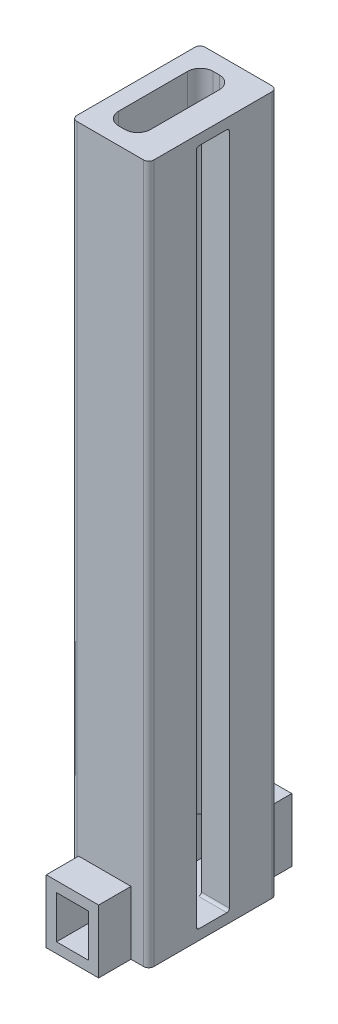
SolidWorks part; units mm, degrees
ref_plane "Front Plane" through (0, 0, 0) normal (0, 0, 1) x (1, 0, 0)
ref_plane "Top Plane" through (0, 0, 0) normal (0, 1, 0) x (1, 0, 0)
ref_plane "Right Plane" through (0, 0, 0) normal (1, 0, 0) x (0, 0, -1)
sketch "Sketch3" plane through (0, 0, 0) normal (0, 1, 0) x (1, 0, 0)
  line L0 (0, -11.5) -> (0, 11.5)
  line L1 (1, 12.5) -> (14, 12.5)
  line L2 (15, 11.5) -> (15, 3.2)
  line L3 (15, 3.2) -> (9.55, 3.2)
  line L4 (9.55, 3.2) -> (9.55, 6.7)
  line L5 (7.05, 9.2) -> (5.85, 9.2)
  line L6 (1, -12.5) -> (14, -12.5)
  line L7 (15, -11.5) -> (15, -3.2)
  line L8 (15, -3.2) -> (9.55, -3.2)
  line L9 (9.55, -3.2) -> (9.55, -6.7)
  line L10 (7.05, -9.2) -> (5.85, -9.2)
  line L11 (3.35, -6.7) -> (3.35, 6.7)
  arc A0 (9.55, -6.7) -> (7.05, -9.2) centre (7.05, -6.7) cw
  arc A1 (9.55, 6.7) -> (7.05, 9.2) centre (7.05, 6.7) ccw
  arc A2 (5.85, 9.2) -> (3.35, 6.7) centre (5.85, 6.7) ccw
  arc A3 (5.85, -9.2) -> (3.35, -6.7) centre (5.85, -6.7) cw
  arc A4 (0, -11.5) -> (1, -12.5) centre (1, -11.5) ccw
  arc A5 (14, -12.5) -> (15, -11.5) centre (14, -11.5) ccw
  arc A6 (14, 12.5) -> (15, 11.5) centre (14, 11.5) cw
  arc A7 (0, 11.5) -> (1, 12.5) centre (1, 11.5) cw
  point P4 (0, 0)
  point P17 (9.55, -9.2)
  point P20 (9.55, 9.2)
  point P23 (3.35, 9.2)
  point P26 (3.35, -9.2)
  point P29 (0, -12.5)
  point P32 (15, -12.5)
  point P35 (15, 12.5)
  point P38 (0, 12.5)
  dimension "D11" = 2.5
  dimension "D12" = 1
  dimension "D1" = 25
  dimension "D2" = 15
  dimension "D3" = 15
  dimension "D4" = 6.2
  dimension "D5" = 6.2
  dimension "D6" = 18.4
  dimension "D7" = 3.3
  dimension "D8" = 6
  dimension "D9" = 6
  dimension "D10" = 3.35
extrude "Boss-Extrude2" add sketch "Sketch3" along normal blind 134
sketch "Sketch6" plane through (0, 0, 0) normal (0, -1, 0) x (1, 0, 0)
  line L0 (1, 12.5) -> (3.35, 12.5)
  line L1 (15, 11.5) -> (15, -11.5)
  line L2 (14, -12.5) -> (9.55, -12.5)
  line L3 (0, -11.5) -> (0, 11.5)
  line L4 (0, -11.5) -> (0, 11.5) construction
  line L5 (6.45, 12.5) -> (6.45, 18.8) construction
  line L7 (6.45, -12.5) -> (6.45, -18.8) construction
  line L8 (1, 12.5) -> (14, 12.5) construction
  line L9 (3.35, 18.8) -> (9.55, 18.8)
  line L10 (9.55, 18.8) -> (9.55, 12.5)
  line L12 (3.35, 18.8) -> (3.35, 12.5)
  line L13 (3.35, -18.8) -> (9.55, -18.8)
  line L14 (9.55, -18.8) -> (9.55, -12.5)
  line L15 (3.35, -18.8) -> (3.35, -12.5)
  line L16 (9.55, 12.5) -> (14, 12.5)
  line L17 (3.35, -12.5) -> (1, -12.5)
  line L18 (3.35, 6.7) -> (3.35, -6.7) construction
  line L19 (9.55, 3.2) -> (9.55, 6.7) construction
  line L20 (9.55, -6.7) -> (9.55, -3.2) construction
  arc A0 (1, -12.5) -> (0, -11.5) centre (1, -11.5) cw
  arc A1 (15, -11.5) -> (14, -12.5) centre (14, -11.5) cw
  arc A2 (14, 12.5) -> (15, 11.5) centre (14, 11.5) cw
  arc A3 (1, 12.5) -> (0, 11.5) centre (1, 11.5) ccw
  point P8 (0, -12.5)
  point P13 (15, 12.5)
  point P16 (0, 12.5)
  point P26 (6.45, 18.8)
  point P31 (6.45, -18.8)
  dimension "D3" = 1
  dimension "D1" = 15
  dimension "D2" = 25
  dimension "D5" = 6.3
  dimension "D7" = 6.3
extrude "Boss-Extrude3" add sketch "Sketch6" along normal blind 2
sketch "Sketch7" plane through (0, 0, 12.5) normal (0, 0, 1) x (1, 0, 0)
  line L0 (3.35, 0) -> (3.35, 8.35)
  line L1 (3.35, 8.35) -> (9.55, 8.35)
  line L2 (9.55, 8.35) -> (9.55, 0)
  line L3 (3.35, 0) -> (9.55, 0)
  dimension "D1" = 8.35
extrude "Cut-Extrude5" [suppressed] cut sketch "Sketch7" against normal through all
sketch "Sketch18" plane through (0, 134, 0) normal (0, 1, 0) x (1, 0, 0)
  line L0 (9.55, 3.2) -> (9.55, -3.2)
  line L1 (9.55, -3.2) -> (15, -3.2)
  line L2 (15, -3.2) -> (15, 3.2)
  line L3 (15, 3.2) -> (9.55, 3.2)
extrude "Boss-Extrude10" add sketch "Sketch18" against normal blind 2
fillet "Fillet1" radius 0.5 1 edges at (12.275, 132, 3.2)
fillet "Fillet2" radius 0.5 3 edges at (12.275, 0, 3.2) (12.275, 132, -3.2) (12.275, 0, -3.2)
sketch "Sketch43" plane through (0, -2, 0) normal (0, 1, 0) x (1, 0, 0)
  line L12 (9.55, 12.5) -> (9.55, 18.8)
  line L13 (9.55, 18.8) -> (3.35, 18.8)
  line L14 (3.35, 18.8) -> (3.35, 12.5)
  line L15 (3.35, 12.5) -> (1, 12.5)
  line L16 (0, 11.5) -> (0, -11.5)
  line L17 (1, -12.5) -> (3.35, -12.5)
  line L18 (3.35, -12.5) -> (3.35, -18.8)
  line L19 (3.35, -18.8) -> (9.55, -18.8)
  line L20 (9.55, -18.8) -> (9.55, -12.5)
  line L21 (9.55, -12.5) -> (14, -12.5)
  line L22 (15, -11.5) -> (15, 11.5)
  line L23 (14, 12.5) -> (9.55, 12.5)
  line L24 (9.55, 12.5) -> (9.55, 18.8)
  line L25 (9.55, 18.8) -> (3.35, 18.8)
  line L26 (3.35, 18.8) -> (3.35, 12.5)
  line L27 (3.35, 12.5) -> (1, 12.5)
  line L28 (0, 11.5) -> (0, -11.5)
  line L29 (1, -12.5) -> (3.35, -12.5)
  line L30 (3.35, -12.5) -> (3.35, -18.8)
  line L31 (3.35, -18.8) -> (9.55, -18.8)
  line L32 (9.55, -18.8) -> (9.55, -12.5)
  line L33 (9.55, -12.5) -> (14, -12.5)
  line L34 (15, -11.5) -> (15, 11.5)
  line L35 (14, 12.5) -> (9.55, 12.5)
  arc A4 (1, 12.5) -> (0, 11.5) centre (1, 11.5) ccw
  arc A5 (0, -11.5) -> (1, -12.5) centre (1, -11.5) ccw
  arc A6 (14, -12.5) -> (15, -11.5) centre (14, -11.5) ccw
  arc A7 (15, 11.5) -> (14, 12.5) centre (14, 11.5) ccw
  arc A8 (1, 12.5) -> (0, 11.5) centre (1, 11.5) ccw
  arc A9 (0, -11.5) -> (1, -12.5) centre (1, -11.5) ccw
  arc A10 (14, -12.5) -> (15, -11.5) centre (14, -11.5) ccw
  arc A11 (15, 11.5) -> (14, 12.5) centre (14, 11.5) ccw
  dimension "D1" = 0
sketch "Sketch44" plane through (0, -2, 0) normal (0, -1, 0) x (1, 0, 0)
sketch "Sketch45" plane through (0, 0, -12.5) normal (0, 0, -1) x (-1, 0, 0)
  line L1 (-9.55, 0) -> (-3.35, 0)
  line L2 (-9.55, 0) -> (-9.55, 8.3)
  line L3 (-9.55, 8.3) -> (-3.35, 8.3)
  line L4 (-3.35, 0) -> (-3.35, 8.3)
  dimension "D1" = 8.3
extrude "Cut-Extrude6" cut sketch "Sketch45" against normal through all
sketch "Sketch46" plane through (0, 0, -12.5) normal (0, 0, -1) x (-1, 0, 0)
  line L0 (-9.55, -2) -> (-9.55, 8.3)
  line L1 (-9.55, 8.3) -> (-3.35, 8.3)
  line L2 (-3.35, 8.3) -> (-3.35, -2)
  line L3 (-11.55, -2) -> (-11.55, 10.3)
  line L4 (-11.55, 10.3) -> (-1.35, 10.3)
  line L5 (-1.35, 10.3) -> (-1.35, -2)
  line L6 (-9.55, -2) -> (-11.55, -2)
  line L7 (-3.35, -2) -> (-1.35, -2)
  dimension "D1" = 2
extrude "Boss-Extrude11" add sketch "Sketch46" along normal blind 6.3
ref_plane "Plane1" through (0, 0, 0) normal (0, 0, -1) x (-1, 0, 0)
mirror "Mirror1" about plane through (0, 0, 0) normal (0, 0, -1) of "Boss-Extrude11"
